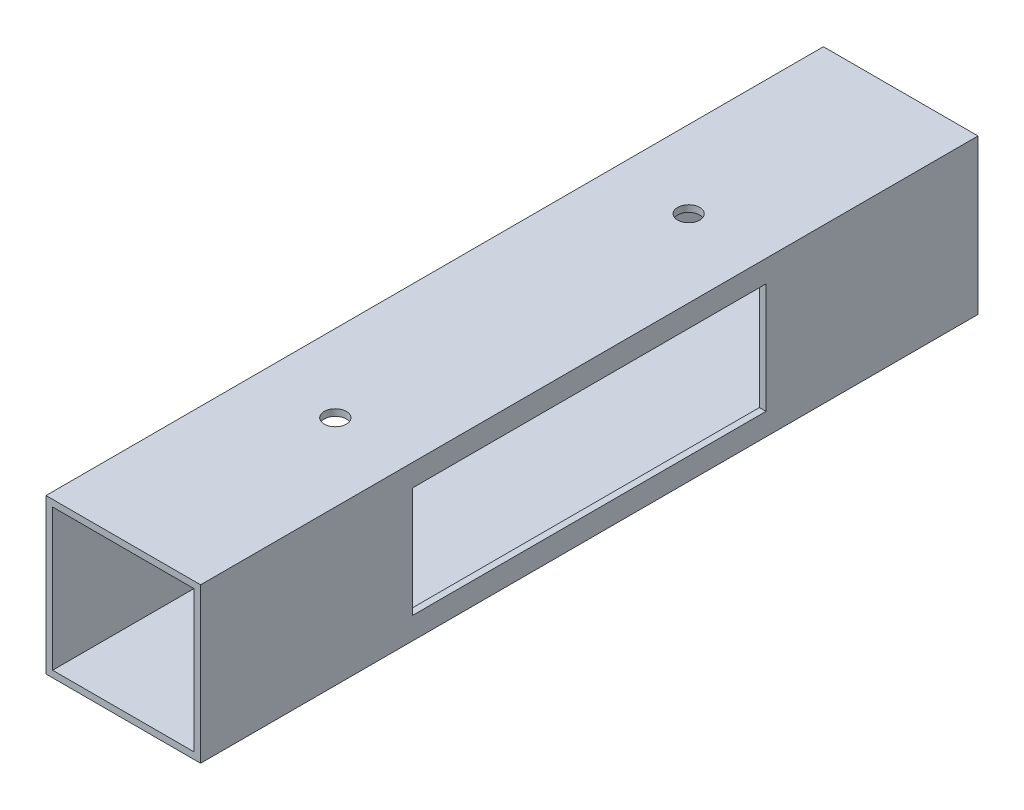
SolidWorks part; units mm, degrees
ref_plane "Plan de face" through (0, 0, 0) normal (0, 0, 1) x (1, 0, 0)
ref_plane "Plan de dessus" through (0, 0, 0) normal (0, 1, 0) x (1, 0, 0)
ref_plane "Plan de droite" through (0, 0, 0) normal (1, 0, 0) x (0, 0, -1)
sketch "MotorBlockSketch" plane through (0, 0, 0) normal (0, 0, 1) x (1, 0, 0)
  line L1 (-17.5, -17.5) -> (17.5, -17.5)
  line L2 (-17.5, -17.5) -> (-17.5, 17.5)
  line L3 (-17.5, 17.5) -> (17.5, 17.5)
  line L4 (17.5, -17.5) -> (17.5, 17.5)
  line L5 (-16, -16) -> (16, -16)
  line L6 (-16, -16) -> (-16, 16)
  line L7 (-16, 16) -> (16, 16)
  line L8 (16, -16) -> (16, 16)
  dimension "D1" = 35
  dimension "D2" = 35
  dimension "D3" = 1.5
  dimension "D4" = 1.5
  dimension "D5" = 32
  dimension "D6" = 17.5
  dimension "D7" = 17.5
extrude "Boss.-Extru.1" add sketch "MotorBlockSketch" along normal mid plane 176
sketch "Esquisse3" plane through (17.5, 0, 0) normal (1, 0, 0) x (0, 0, -1)
  line L0 (-88, 17.5) -> (88, 17.5) construction
  line L1 (-40, 12.5) -> (40, 12.5)
  line L2 (-40, 12.5) -> (-40, -12.5)
  line L3 (-40, -12.5) -> (40, -12.5)
  line L4 (40, 12.5) -> (40, -12.5)
  line L5 (-88, -17.5) -> (88, -17.5) construction
  line L7 (0, 19.25) -> (0, -19.25) construction
  dimension "D1" = 80
  dimension "D2" = 5
  dimension "D3" = 5
  dimension "D4" = 40
extrude "Enlèv. mat.-Extru.1" cut sketch "Esquisse3" against normal through all
sketch "DrillLeftMotorFixSketch" plane through (0, 17.5, 0) normal (0, 1, 0) x (1, 0, 0)
  line L0 (-19.25, 0) -> (19.25, 0) construction
  circle A0 centre (0, 40) radius 2.5
  dimension "D1" = 5
  dimension "D2" = 40
extrude "Enlèv. mat.-Extru.2" cut sketch "DrillLeftMotorFixSketch" against normal blind 5
sketch "DrillRightMotorFixSketch" plane through (0, 17.5, 0) normal (0, 1, 0) x (1, 0, 0)
  line L2 (0, -19.25) -> (0, 19.25) construction
  circle A0 centre (0, -40) radius 2.5
  dimension "D1" = 5
  dimension "D2" = 40
extrude "Enlèv. mat.-Extru.3" cut sketch "DrillRightMotorFixSketch" against normal blind 5
